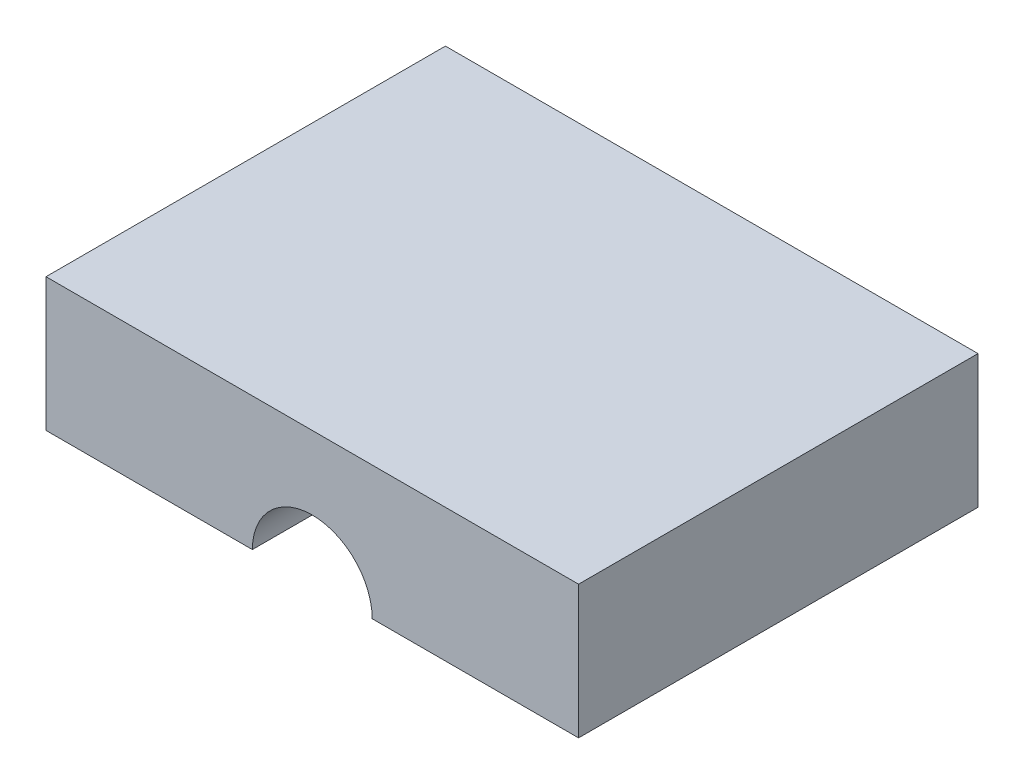
SolidWorks part; units mm, degrees
material "ABS"
ref_plane "Plan de face" through (0, 0, 0) normal (0, 0, 1) x (1, 0, 0)
ref_plane "Plan de dessus" through (0, 0, 0) normal (0, 1, 0) x (1, 0, 0)
ref_plane "Plan de droite" through (0, 0, 0) normal (1, 0, 0) x (0, 0, -1)
sketch "Esquisse1" plane through (0, 0, 0) normal (0, 0, 1) x (1, 0, 0)
  line L1 (0, 0) -> (-20, 0)
  line L2 (0, 0) -> (0, 30)
  line L3 (0, 30) -> (-20, 30)
  line L4 (-20, 0) -> (-20, 30)
  dimension "D1" = 20
  dimension "D2" = 30
extrude "Boss.-Extru.1" add sketch "Esquisse1" along normal blind 10
sketch "Esquisse2" plane through (0, 0, 10) normal (0, 0, 1) x (1, 0, 0)
  line L0 (-10, 0) -> (-10, 30) construction
  line L1 (-20, 0) -> (0, 0) construction
  line L2 (0, 30) -> (-20, 30) construction
  line L3 (-20, 0) -> (-20, 18) construction
  line L4 (-20, 30) -> (-20, 0) construction
  line L5 (-20, 18) -> (0, 18) construction
  line L6 (0, 0) -> (0, 30) construction
  circle A0 centre (-10, 18) radius 6
  dimension "D2" = 12
  dimension "D1" = 18
extrude "Boss.-Extru.2" add sketch "Esquisse2" along normal blind 40
sketch "Esquisse3" plane through (0, 0, 0) normal (0, -1, 0) x (1, 0, 0)
  line L0 (-10, 0) -> (10, 0) construction
  line L1 (-20, 0) -> (0, 0) construction
  line L2 (-10, 0) -> (-30, 0) construction
  line L4 (10, 0) -> (-30, 0)
  line L5 (10, 0) -> (10, 30)
  line L6 (10, 30) -> (-30, 30)
  line L7 (-30, 0) -> (-30, 30)
  dimension "D1" = 20
  dimension "D2" = 20
  dimension "D3" = 30
extrude "Boss.-Extru.3" add sketch "Esquisse3" along normal blind 15
sketch "Esquisse4" plane through (0, 0, 0) normal (0, 0, -1) x (-1, 0, 0)
  line L0 (30, -15) -> (-10, -15) construction
  circle A0 centre (10, -15) radius 4.5
  dimension "D1" = 9
extrude "Enlèv. mat.-Extru.1" cut sketch "Esquisse4" against normal blind 55
sketch "Esquisse5" plane through (0, 0, 0) normal (0, 0, -1) x (-1, 0, 0)
  line L0 (-2.25, -15) -> (-5, -15)
  line L1 (5.5, -15) -> (-10, -15) construction
  line L2 (-10, -10) -> (-10, -5)
  line L3 (-5, 0) -> (25, 0)
  line L4 (30, -5) -> (30, -10)
  line L5 (25, -15) -> (20.9044, -15)
  line L6 (30, -15) -> (14.5, -15) construction
  line L7 (-2.25, -15) -> (-10, -15)
  line L8 (-10, -15) -> (-10, 0)
  line L9 (-10, 0) -> (30, 0)
  line L10 (30, 0) -> (30, -15)
  line L11 (30, -15) -> (20.9044, -15)
  arc A0 (25, -15) -> (30, -10) centre (25, -10) ccw
  arc A1 (30, -5) -> (25, 0) centre (25, -5) ccw
  arc A2 (-5, -15) -> (-10, -10) centre (-5, -10) cw
  arc A3 (-10, -5) -> (-5, 0) centre (-5, -5) cw
  point P16 (30, -15)
  point P19 (30, 0)
  point P22 (-10, -15)
  point P25 (-10, 0)
  line M18 (30, -15) -> (30, 0)
  line M19 (30, 0) -> (20, 0)
  line M23 (0, 0) -> (-10, 0)
  line M24 (-10, 0) -> (-10, -15)
  dimension "D1" = 5
extrude "Enlèv. mat.-Extru.3" cut sketch "Esquisse5" against normal blind 55 contours A1 M18 M19 | A3 M24 M23
sketch "Esquisse8" plane through (0, 0, 0) normal (0, 0, -1) x (-1, 0, 0)
  line L1 (-10, -5) -> (30.2666, -5)
  line L2 (-10, -5) -> (-10, 31.2123)
  line L3 (-10, 31.2123) -> (30.2666, 31.2123)
  line L4 (30.2666, -5) -> (30.2666, 31.2123)
extrude "Enlèv. mat.-Extru.4" cut sketch "Esquisse8" against normal blind 55
